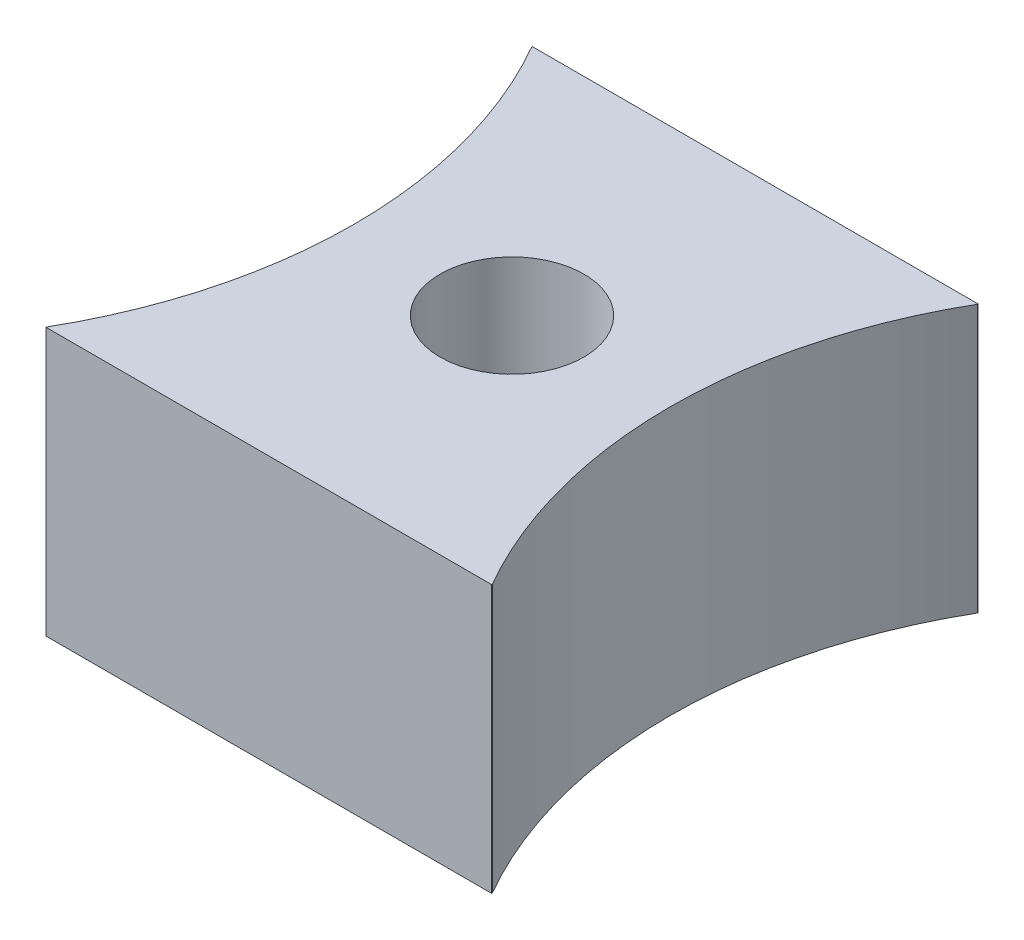
SolidWorks part; units mm, degrees
material "3003 Alloy"
ref_plane "Front Plane" through (0, 0, 0) normal (0, 0, 1) x (1, 0, 0)
ref_plane "Top Plane" through (0, 0, 0) normal (0, 1, 0) x (1, 0, 0)
ref_plane "Right Plane" through (0, 0, 0) normal (1, 0, 0) x (0, 0, -1)
sketch "Sketch1" plane through (0, 0, 0) normal (0, 1, 0) x (1, 0, 0)
  line L0 (0, 0) -> (11, -12) construction
  line L1 (0, 0) -> (11, 0)
  line L2 (0, 0) -> (0, -12)
  line L3 (0, -12) -> (11, -12)
  line L4 (11, 0) -> (11, -12)
  line L5 (0, -12) -> (11, 0) construction
  dimension "D1" = 11
  dimension "D2" = 12
extrude "Boss-Extrude1" add sketch "Sketch1" along normal blind 6.6
sketch "Sketch2" plane through (0, 6.6, 0) normal (0, 1, 0) x (1, 0, 0)
  line L0 (0, 0) -> (1.6, 0)
  line L1 (11, 0) -> (0, 0) construction
  line L3 (0, -12) -> (11, -12) construction
  line L4 (5.5, 0) -> (5.5, -12) construction
  line L6 (0, 0) -> (0, -12) construction
  line L7 (0, 0) -> (0, -12)
  arc A0 (0, -11.9867) -> (0, -0.0133) centre (-10.4, -6) ccw
  arc A1 (11, -11.9867) -> (11, -0.0133) centre (21.4, -6) cw
  circle A2 centre (5.5, -6) radius 1.775
  line M10 (11, -12) -> (11, 0)
  dimension "D2" = 3.55
  dimension "D1" = 1.6
extrude "Cut-Extrude1" cut sketch "Sketch2" against normal blind 6.6 contours A1 M10 | L7 A0 | L4 A2 | A2 L4
